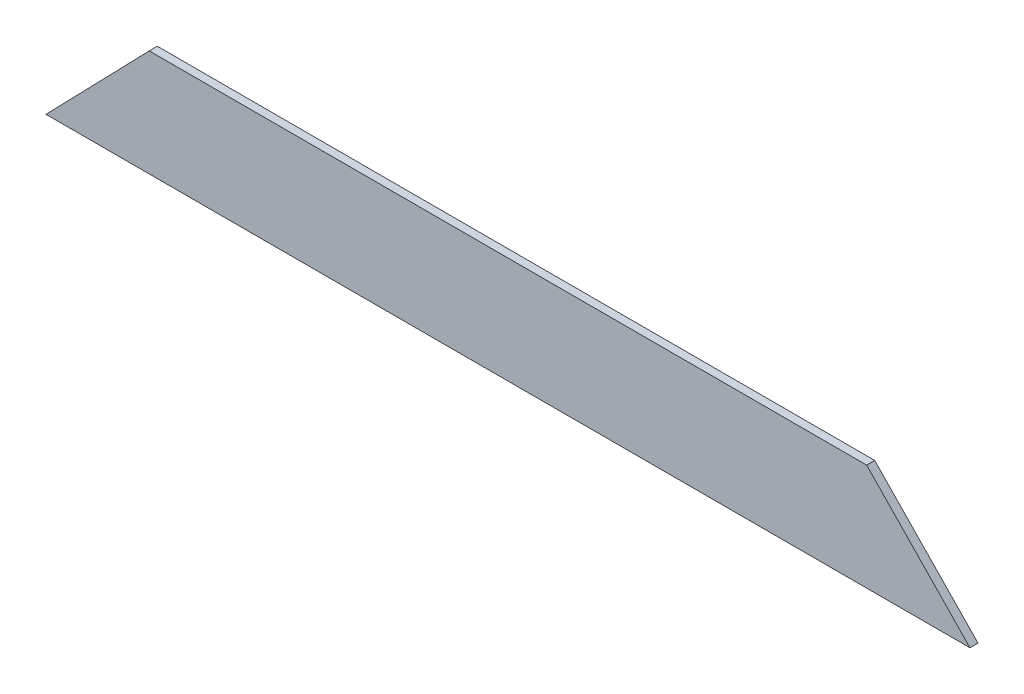
SolidWorks part; units mm, degrees
material "Pine"
ref_plane "Front Plane" through (0, 0, 0) normal (0, 0, 1) x (1, 0, 0)
ref_plane "Top Plane" through (0, 0, 0) normal (0, 1, 0) x (1, 0, 0)
ref_plane "Right Plane" through (0, 0, 0) normal (1, 0, 0) x (0, 0, -1)
sketch "Sketch1" plane through (0, 0, 0) normal (0, 0, 1) x (1, 0, 0)
  line L0 (1226.805, 308.7761) -> (992.969, 550.0761)
  line L1 (-631.2816, 550.0761) -> (992.969, 550.0761)
  line L3 (-681.751, 308.7761) -> (1226.805, 308.7761)
  line L5 (180.8437, 550.0761) -> (180.8437, 269.3807) construction
  line L9 (-631.2816, 550.0761) -> (-865.1176, 308.7761)
  line L12 (-681.751, 308.7761) -> (-865.1176, 308.7761)
  dimension "D1" = 1908.556
  dimension "D2" = 241.3
  dimension "D3" = 45.9
  dimension "D4" = 1624.2506
  dimension "D5" = 45.9
extrude "Boss-Extrude1" add sketch "Sketch1" along normal blind 18.2562
chamfer "Chamfer1" [suppressed] distance 63.5 angle 15
